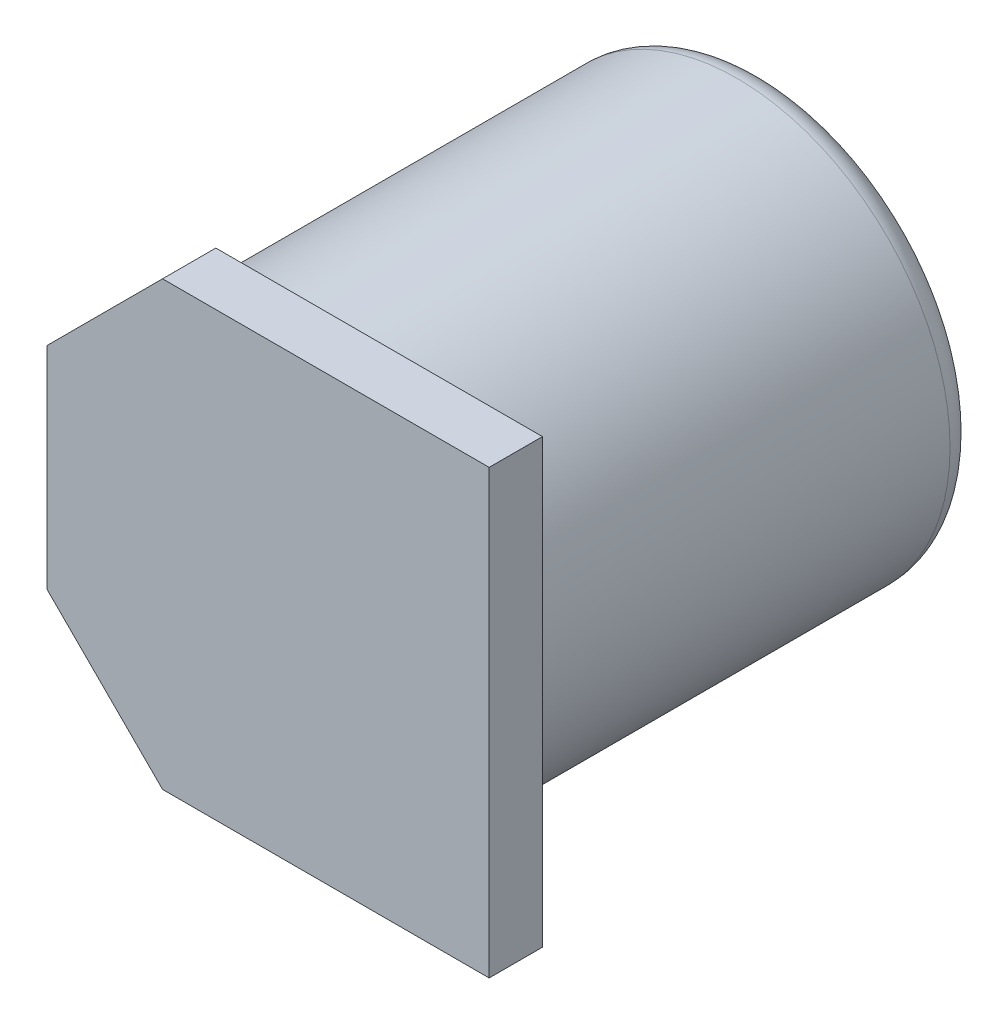
SolidWorks part; units mm, degrees
ref_plane "Front Plane" through (0, 0, 0) normal (0, 0, 1) x (1, 0, 0)
ref_plane "Top Plane" through (0, 0, 0) normal (0, 1, 0) x (1, 0, 0)
ref_plane "Right Plane" through (0, 0, 0) normal (1, 0, 0) x (0, 0, -1)
sketch "Sketch1" plane through (0, 0, 0) normal (0, 0, 1) x (1, 0, 0)
  line L0 (-4.15, 1.98) -> (-1.98, 4.15)
  line L1 (-1.98, 4.15) -> (4.15, 4.15)
  line L2 (-4.15, 1.98) -> (-4.15, -1.98)
  line L3 (-1.98, -4.15) -> (4.15, -4.15)
  line L4 (4.15, 4.15) -> (4.15, -4.15)
  line L5 (-4.15, 4.15) -> (4.15, -4.15) construction
  line L6 (-4.15, -4.15) -> (4.15, 4.15) construction
  line L7 (-4.15, -1.98) -> (-1.98, -4.15)
  point P0 (0, 0)
  dimension "D1" = 8.3
  dimension "D2" = 8.3
extrude "Boss-Extrude1" add sketch "Sketch1" along normal blind 1
sketch "Sketch2" plane through (0, 0, 0) normal (0, 0, 1) x (1, 0, 0)
  circle A0 centre (0, 0) radius 4
  dimension "D1" = 8
extrude "Boss-Extrude2" add sketch "Sketch2" against normal blind 8.3
fillet "Fillet2" radius 0.5 1 edges at (4, 0, -8.3)
